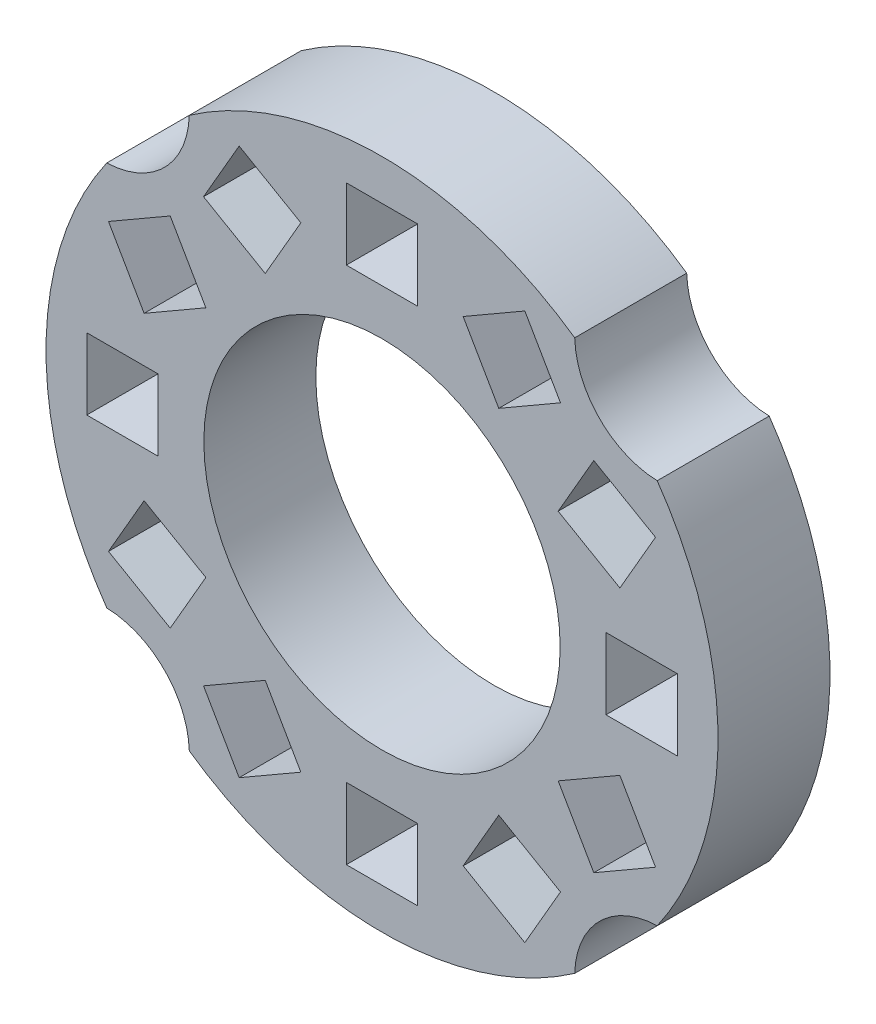
SolidWorks part; units mm, degrees
ref_plane "Front Plane" through (0, 0, 0) normal (0, 0, 1) x (1, 0, 0)
ref_plane "Top Plane" through (0, 0, 0) normal (0, 1, 0) x (1, 0, 0)
ref_plane "Right Plane" through (0, 0, 0) normal (1, 0, 0) x (0, 0, -1)
sketch "Sketch1" plane through (0, 0, 0) normal (0, 0, 1) x (1, 0, 0)
  line L0 (0, -40.3076) -> (0, 40.3076) construction
  line L5 (0, 0) -> (22.0836, 12.75) construction
  line L6 (0, 0) -> (12.75, 22.0836) construction
  line L7 (-37.9287, 0) -> (37.9287, 0) construction
  line L8 (17.3026, 11.4689) -> (20.8026, 17.5311)
  line L9 (17.3026, 11.4689) -> (23.3647, 7.9689)
  line L10 (23.3647, 7.9689) -> (26.8647, 14.0311)
  line L11 (20.8026, 17.5311) -> (26.8647, 14.0311)
  line L12 (17.3026, 11.4689) -> (26.8647, 14.0311) construction
  line L13 (23.3647, 7.9689) -> (20.8026, 17.5311) construction
  line L14 (22, 3.5) -> (29, 3.5)
  line L15 (22, 3.5) -> (22, -3.5)
  line L16 (22, -3.5) -> (29, -3.5)
  line L17 (29, 3.5) -> (29, -3.5)
  line L18 (22, 3.5) -> (29, -3.5) construction
  line L19 (22, -3.5) -> (29, 3.5) construction
  line L20 (7.9689, 23.3647) -> (14.0311, 26.8647)
  line L21 (7.9689, 23.3647) -> (11.4689, 17.3026)
  line L22 (11.4689, 17.3026) -> (17.5311, 20.8026)
  line L23 (14.0311, 26.8647) -> (17.5311, 20.8026)
  line L24 (7.9689, 23.3647) -> (17.5311, 20.8026) construction
  line L25 (11.4689, 17.3026) -> (14.0311, 26.8647) construction
  line L26 (0, 0) -> (0, 25.5) construction
  line L27 (-3.5, 29) -> (3.5, 29)
  line L28 (-3.5, 29) -> (-3.5, 22)
  line L29 (-3.5, 22) -> (3.5, 22)
  line L30 (3.5, 29) -> (3.5, 22)
  line L31 (-3.5, 29) -> (3.5, 22) construction
  line L32 (-3.5, 22) -> (3.5, 29) construction
  line L33 (-22, -3.5) -> (-29, -3.5)
  line L34 (-29, 3.5) -> (-29, -3.5)
  line L35 (-22, 3.5) -> (-29, 3.5)
  line L36 (-22, 3.5) -> (-22, -3.5)
  line L37 (-23.3647, 7.9689) -> (-26.8647, 14.0311)
  line L38 (-20.8026, 17.5311) -> (-26.8647, 14.0311)
  line L39 (-17.3026, 11.4689) -> (-20.8026, 17.5311)
  line L40 (-17.3026, 11.4689) -> (-23.3647, 7.9689)
  line L41 (-11.4689, 17.3026) -> (-17.5311, 20.8026)
  line L42 (-14.0311, 26.8647) -> (-17.5311, 20.8026)
  line L43 (-7.9689, 23.3647) -> (-14.0311, 26.8647)
  line L44 (-7.9689, 23.3647) -> (-11.4689, 17.3026)
  line L45 (23.3647, -7.9689) -> (26.8647, -14.0311)
  line L46 (20.8026, -17.5311) -> (26.8647, -14.0311)
  line L47 (17.3026, -11.4689) -> (20.8026, -17.5311)
  line L48 (17.3026, -11.4689) -> (23.3647, -7.9689)
  line L49 (11.4689, -17.3026) -> (17.5311, -20.8026)
  line L50 (14.0311, -26.8647) -> (17.5311, -20.8026)
  line L51 (7.9689, -23.3647) -> (14.0311, -26.8647)
  line L52 (7.9689, -23.3647) -> (11.4689, -17.3026)
  line L53 (-3.5, -22) -> (3.5, -22)
  line L54 (3.5, -29) -> (3.5, -22)
  line L55 (-3.5, -29) -> (3.5, -29)
  line L56 (-3.5, -29) -> (-3.5, -22)
  line L57 (-7.9689, -23.3647) -> (-11.4689, -17.3026)
  line L58 (-7.9689, -23.3647) -> (-14.0311, -26.8647)
  line L59 (-14.0311, -26.8647) -> (-17.5311, -20.8026)
  line L60 (-11.4689, -17.3026) -> (-17.5311, -20.8026)
  line L61 (-17.3026, -11.4689) -> (-23.3647, -7.9689)
  line L62 (-17.3026, -11.4689) -> (-20.8026, -17.5311)
  line L63 (-20.8026, -17.5311) -> (-26.8647, -14.0311)
  line L64 (-23.3647, -7.9689) -> (-26.8647, -14.0311)
  circle A0 centre (0, 0) radius 33
  circle A1 centre (0, 0) radius 25.5 construction
  circle A2 centre (0, 0) radius 17.5
  point P11 (0, 0)
  point P14 (0, 0)
  point P15 (25.5, 0)
  point P22 (0, 25.5)
  point P26 (12.75, 22.0836)
  dimension "D1" = 66
  dimension "D3" = 51
  dimension "D17" = 35
  dimension "D2" = 30
  dimension "D6" = 7
  dimension "D7" = 7
  dimension "D4" = 7
  dimension "D5" = 7
  dimension "D8" = 105
  dimension "D9" = 7
  dimension "D10" = 7
  dimension "D11" = 75
  dimension "D12" = 60
  dimension "D13" = 7
  dimension "D14" = 7
  dimension "D15" = 45
  dimension "D16" = 90
extrude "Boss-Extrude1" add sketch "Sketch1" along normal blind 11
sketch "Sketch2" plane through (0, 0, 11) normal (0, 0, 1) x (1, 0, 0)
  line L0 (0, 0) -> (-27.032, 18.928) construction
  line L1 (-45.9882, 0) -> (45.9882, 0) construction
  line L2 (0, -35.6846) -> (0, 35.6846) construction
  line L3 (0, 0) -> (-18.928, 27.032) construction
  circle A0 centre (0, 0) radius 33 construction
  arc A1 (-27.032, 18.928) -> (-18.928, 27.032) centre (-27.2741, 27.2741) ccw
  point P9 (0, 0)
  point P11 (0, 0)
  dimension "D3" = 8.3496
  dimension "D1" = 35
  dimension "D2" = 55
extrude "Cut-Extrude1" cut sketch "Sketch2" against normal through all both and the other way through all contours A1
mirror "Mirror1" about plane through (0, 0, 0) normal (1, 0, 0) of "Cut-Extrude1"
mirror "Mirror2" about plane through (0, 0, 0) normal (0, 1, 0) of "Mirror1", "Cut-Extrude1"
equation "\"size\"= 0.7"
equation "\"D7@Sketch1\"=\"size\""
equation "\"D6@Sketch1\"=\"size\""
equation "\"D4@Sketch1\"=\"size\""
equation "\"D5@Sketch1\"=\"size\""
equation "\"squares_radius\"= 5.1"
equation "\"D3@Sketch1\"=\"squares_radius\""
equation "\"D9@Sketch1\"=\"size\""
equation "\"D10@Sketch1\"=\"size\""
equation "\"D13@Sketch1\"=\"size\""
equation "\"D14@Sketch1\"=\"size\""
equation "\"inner_radius\"= 3.5"
equation "\"D17@Sketch1\"=\"inner_radius\""
equation "\"outer_radius\"= 6.6"
equation "\"D1@Sketch1\"=\"outer_radius\""
